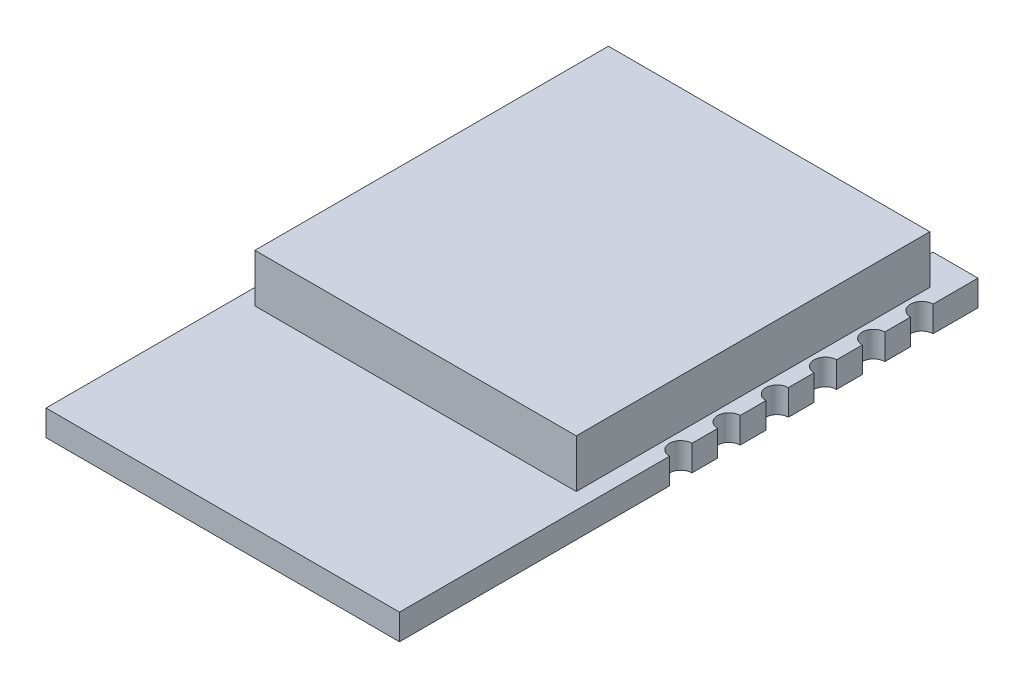
SolidWorks part; units mm, degrees
ref_plane "前视基准面" through (0, 0, 0) normal (0, 0, 1) x (1, 0, 0)
ref_plane "上视基准面" through (0, 0, 0) normal (0, 1, 0) x (1, 0, 0)
ref_plane "右视基准面" through (0, 0, 0) normal (1, 0, 0) x (0, 0, -1)
other "Configuration Table"
sketch "草图2" plane through (0, 0, 0) normal (0, 1, 0) x (1, 0, 0)
  line L1 (-5.5, 9) -> (5.5, 9)
  line L2 (-5.5, 9) -> (-5.5, -9)
  line L3 (-5.5, -9) -> (5.5, -9)
  line L4 (5.5, 9) -> (5.5, -9)
  line L5 (-5.5, 9) -> (5.5, -9) construction
  line L6 (-5.5, -9) -> (5.5, 9) construction
  point P0 (0, 0)
  dimension "D1" = 11
extrude "凸台-拉伸1" add sketch "草图2" along normal blind 0.8
sketch "草图3" plane through (0, 0, 0) normal (0, 1, 0) x (1, 0, 0)
  line L6 (-5, -3) -> (5, -3)
  line L7 (-5, -3) -> (-5, 8)
  line L8 (-5, 8) -> (5, 8)
  line L9 (5, -3) -> (5, 8)
  dimension "D1" = 11
extrude "凸台-拉伸3" add sketch "草图3" along normal blind 2.3
sketch "草图7" plane through (0, 0.8, 0) normal (0, 1, 0) x (1, 0, 0)
  circle A0 centre (-3.75, 9) radius 0.35
extrude "切除-拉伸1" cut sketch "草图7" against normal blind 2.3
sketch "草图9" plane through (0, 0, 0) normal (0, 1, 0) x (1, 0, 0)
  circle A0 centre (-2.25, 9) radius 0.35
  circle A1 centre (-0.75, 9) radius 0.35
  circle A2 centre (0.75, 9) radius 0.35
  circle A3 centre (3.75, 9) radius 0.35
  circle A4 centre (2.25, 9) radius 0.35
extrude "切除-拉伸2" cut sketch "草图9" against normal blind 2.3 and the other way blind 2.3
sketch "草图10" plane through (0, 0, 0) normal (0, 1, 0) x (1, 0, 0)
  circle A0 centre (-5.5, 7.25) radius 0.35
  circle A1 centre (5.5, 7.25) radius 0.35
  circle A2 centre (5.5, -0.25) radius 0.35
  circle A3 centre (-5.5, 2.75) radius 0.35
  circle A4 centre (5.5, 5.75) radius 0.35
  circle A5 centre (-5.5, 4.25) radius 0.35
  circle A6 centre (5.5, 2.75) radius 0.35
  circle A7 centre (-5.5, 5.75) radius 0.35
  circle A8 centre (5.5, 4.25) radius 0.35
  circle A9 centre (5.5, 1.25) radius 0.35
  circle A10 centre (-5.5, 1.25) radius 0.35
  circle A11 centre (-5.5, -0.25) radius 0.35
  point P24 (0, 0)
  point P25 (0, 0)
  point P26 (0, 0)
extrude "切除-拉伸5" cut sketch "草图10" against normal blind 2.3 and the other way blind 2.3 contours A1 | A4 | A6 | A2 | A3 | A0 | A5 | A7 | A8 | A9 | A11 | A10
